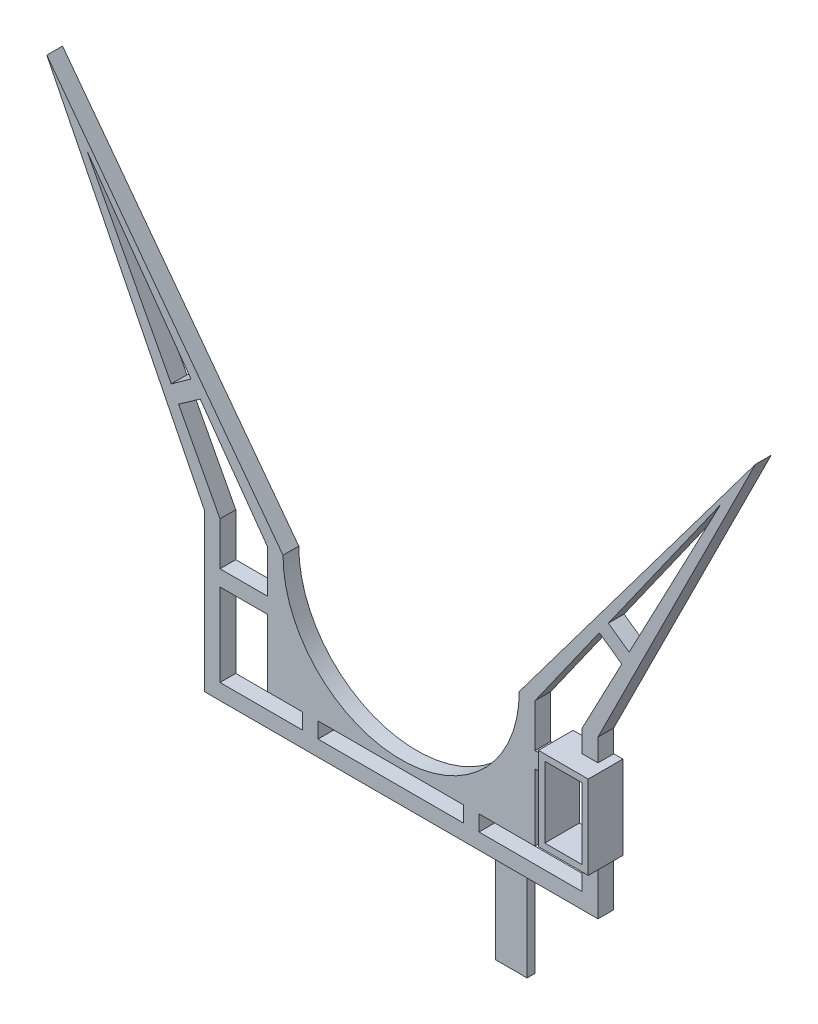
SolidWorks part; units mm, degrees
ref_plane "Front Plane" through (0, 0, 0) normal (0, 0, 1) x (1, 0, 0)
ref_plane "Top Plane" through (0, 0, 0) normal (0, 1, 0) x (1, 0, 0)
ref_plane "Right Plane" through (0, 0, 0) normal (1, 0, 0) x (0, 0, -1)
sketch "Sketch1" plane through (0, 0, 0) normal (0, 0, 1) x (1, 0, 0)
  line L0 (-112.5, 125) -> (-62.5, 25)
  line L1 (-62.5, -25) -> (62.5, -25)
  line L2 (-62.5, -25) -> (-62.5, 25)
  line L3 (-62.5, 25) -> (62.5, 25)
  line L4 (62.5, -25) -> (62.5, 25)
  line L5 (-62.5, -25) -> (62.5, 25) construction
  line L6 (-62.5, 25) -> (62.5, -25) construction
  line L7 (-37.5, 25) -> (-112.5, 25)
  line L8 (-37.5, 25) -> (-37.5, 125)
  line L9 (-37.5, 125) -> (-112.5, 125)
  line L10 (-112.5, 25) -> (-112.5, 125)
  line L11 (37.5, 25) -> (112.5, 25)
  line L12 (37.5, 25) -> (37.5, 125)
  line L13 (37.5, 125) -> (112.5, 125)
  line L14 (112.5, 25) -> (112.5, 125)
  line L15 (-112.5, 125) -> (-37.5, 25)
  line L16 (37.5, 25) -> (112.5, 125)
  line L17 (62.5, 25) -> (112.5, 125)
  arc A0 (37.5, 25) -> (-37.5, 25) centre (0, 25) cw
  point P0 (0, 0)
  dimension "D5" = 25
  dimension "D1" = 50
  dimension "D2" = 125
  dimension "D3" = 25
  dimension "D4" = 75
  dimension "D6" = 100
  dimension "D7" = 75
  dimension "D8" = 100
  dimension "D9" = 75
extrude "Boss-Extrude1" add sketch "Sketch1" along normal blind 5 contours L15 L0 L3 | L3 A0 L2 L1 L4 | L3 L17 L16
sketch "Sketch2" plane through (0, 0, 5) normal (0, 0, 1) x (1, 0, 0)
  line L10 (101.4139, 108.3538) -> (103.4554, 106.9108)
  line L15 (-42.5, -15) -> (42.5, -15)
  line L20 (57.5, -20) -> (-57.5, -20)
  line L21 (-62.5, -25) -> (62.5, -25) construction
  line L22 (-62.5, 25) -> (-37.5, 25)
  line L23 (37.5, 25) -> (62.5, 25)
  line L24 (-57.5, -20) -> (-57.5, 25)
  line L25 (-57.5, 25) -> (-99.7066, 105)
  line L26 (-99.7066, 105) -> (-42.5, 25)
  line L27 (-42.5, 25) -> (-42.5, -15)
  line L28 (42.5, -15) -> (42.5, 25)
  line L29 (42.5, 25) -> (101.4139, 108.3538)
  line L30 (101.4139, 108.3538) -> (57.5, 25)
  line L31 (57.5, 25) -> (57.5, -20)
  line L32 (-99.7066, 105) -> (-112.5, 125)
  line L33 (-99.7066, 105) -> (-101.9806, 103.9613)
  line L35 (-99.7066, 105) -> (-98.1256, 105.8341)
  line L36 (-112.5, 125) -> (-37.5, 25) construction
  line L37 (101.4139, 108.3538) -> (112.5, 125)
  line L38 (62.5, 25) -> (112.5, 125) construction
  line L40 (-112.5, 125) -> (-62.5, 25) construction
  dimension "D1" = 5
  dimension "D2" = 20
  dimension "D3" = 115
  dimension "D4" = 15
  dimension "D5" = 5
  dimension "D6" = 5
  dimension "D7" = 20
  dimension "D8" = 2.5
  dimension "D9" = 2.5
  dimension "D10" = 40
extrude "Cut-Extrude1" cut sketch "Sketch2" against normal blind 10 contours L31 L23 L28 L15 L27 L22 L24 L20 | L26 L25 L22 | L30 L29 L23
sketch "Sketch3" plane through (0, 0, 5) normal (0, 0, 1) x (1, 0, 0)
  line L0 (-42.5, -15) -> (42.5, -15) construction
  line L1 (-31.3776, -15) -> (-26.3776, -15)
  line L2 (-31.3776, -15) -> (-31.3776, -20)
  line L3 (-31.3776, -20) -> (-26.3776, -20)
  line L4 (-26.3776, -15) -> (-26.3776, -20)
  line L5 (57.5, -20) -> (-57.5, -20) construction
  line L6 (42.5, -15) -> (42.5, 25) construction
  line L7 (19.7255, -15) -> (24.7255, -15)
  line L8 (19.7255, -15) -> (19.7255, -20)
  line L9 (19.7255, -20) -> (24.7255, -20)
  line L10 (24.7255, -15) -> (24.7255, -20)
  line L11 (42.5, 11.2623) -> (57.5, 11.2623)
  line L12 (42.5, 11.2623) -> (42.5, 6.2623)
  line L13 (42.5, 6.2623) -> (57.5, 6.2623)
  line L14 (57.5, 11.2623) -> (57.5, 6.2623)
  line L15 (57.5, 25) -> (57.5, -20) construction
  line L16 (-57.5, -20) -> (-57.5, 25) construction
  line L17 (-57.5, 11.2623) -> (-42.5, 11.2623)
  line L18 (-57.5, 11.2623) -> (-57.5, 6.2623)
  line L19 (-57.5, 6.2623) -> (-42.5, 6.2623)
  line L20 (-42.5, 11.2623) -> (-42.5, 6.2623)
  line L21 (-42.5, 25) -> (-42.5, -15) construction
  line L22 (-70.6543, 49.9331) -> (-63.796, 54.7812)
  line L23 (-57.5, 25) -> (-99.7066, 105) construction
  line L24 (-99.7066, 105) -> (-42.5, 25) construction
  line L25 (-63.796, 54.7812) -> (-66.7044, 58.8483)
  line L26 (-66.7044, 58.8483) -> (-72.9874, 54.3554)
  line L27 (-72.9874, 54.3554) -> (-70.6543, 49.9331)
  line L28 (65.7866, 57.9469) -> (62.9252, 53.8984)
  line L30 (42.5, 25) -> (101.4139, 108.3538) construction
  line L32 (62.9252, 53.8984) -> (70.0659, 48.8515)
  line L33 (101.4139, 108.3538) -> (57.5, 25) construction
  line L34 (70.0659, 48.8515) -> (72.3964, 53.2751)
  line L35 (72.3964, 53.2751) -> (65.7866, 57.9469)
  dimension "D1" = 5
  dimension "D2" = 5
  dimension "D3" = 5
  dimension "D4" = 5
  dimension "D5" = 5
  dimension "D6" = 5
  dimension "D7" = 5
extrude "Boss-Extrude2" add sketch "Sketch3" against normal blind 5
sketch "Sketch5" plane through (0, 0, 0) normal (0, 0, -1) x (-1, 0, 0)
  line L5 (-37.5, -25) -> (-69, -25)
  line L6 (62.5, -25) -> (-62.5, -25) construction
  line L7 (-37.5, -25) -> (-37.5, -55)
  line L8 (-37.5, -55) -> (-69, -55)
  line L9 (-24.7255, -25) -> (-19.7255, -25)
  line L13 (-69, -25) -> (-69, -55)
  line L14 (-59, -25) -> (-27.5, -25)
  line L15 (-59, -25) -> (-59, -55)
  line L16 (-59, -55) -> (-27.5, -55)
  line L17 (31.3776, -25) -> (26.3776, -25)
  line L18 (-27.5, -25) -> (-27.5, -55)
  line L19 (62.5, -25) -> (-62.5, -25)
  dimension "D1" = 10
  dimension "D2" = 31.5
  dimension "D3" = 31.5
  dimension "D4" = 30
  dimension "D5" = 30
  dimension "D6" = 125
  dimension "D7" = 25
extrude "Boss-Extrude3" add sketch "Sketch5" against normal blind 2.5
sketch "Sketch6" plane through (0, 0, 5) normal (0, 0, 1) x (1, 0, 0)
  line L0 (37.5, 25) -> (37.5, 10)
  line L1 (37.5, 10) -> (57.5, 10)
  line L8 (63.4, 10) -> (57.5, 10)
  line L9 (51.6, 15.9) -> (63.4, 15.9)
  line L10 (51.6, 15.9) -> (51.6, -6.6)
  line L11 (51.6, -6.6) -> (63.4, -6.6)
  line L12 (63.4, 15.9) -> (63.4, -6.6)
  line L13 (57.5, 10) -> (51.6, 10)
  line L14 (49.6, 17.9) -> (65.4, 17.9)
  line L15 (49.6, 17.9) -> (49.6, -8.6)
  line L16 (49.6, -8.6) -> (65.4, -8.6)
  line L17 (65.4, 17.9) -> (65.4, -8.6)
  line M18 (57.5, 25) -> (57.5, 11.2623)
  line M19 (57.5, 11.2623) -> (42.5, 11.2623)
  line M40 (42.5, 6.2623) -> (57.5, 6.2623)
  line M41 (57.5, 6.2623) -> (57.5, -20)
  line M50 (62.5, -25) -> (62.5, 25)
  dimension "D1" = 15
  dimension "D2" = 20
  dimension "D3" = 5.9
  dimension "D4" = 5.9
  dimension "D5" = 5.9
  dimension "D6" = 16.6
  dimension "D7" = 2
  dimension "D8" = 2
  dimension "D9" = 2
  dimension "D10" = 2
extrude "Boss-Extrude6" add sketch "Sketch6" against normal blind 5 contours L9 L10 M19 M18 | L10 L1 L8 L9 M19 M50 M18 | L11 L8 L1 L10 M41 M50 M40 | L10 L11 M41 M40 | L17 L14 L9 L12 L11 L16 M50 | L14 L9 M18 M50 | L14 L15 L10 L9 M19 M18 | L15 L16 L11 L10 M41 M40 | L16 L11 M41 M50 | L1 L15 L10 M40 | L15 L1 L10 M19
sketch "Sketch7" plane through (0, 0, 5) normal (0, 0, 1) x (1, 0, 0)
  line L1 (62.5, 15.9) -> (63.4, 15.9)
  line L2 (62.5, 15.9) -> (62.5, -6.6)
  line L3 (62.5, -6.6) -> (63.4, -6.6)
  line L4 (63.4, 15.9) -> (63.4, -6.6)
extrude "Boss-Extrude7" add sketch "Sketch7" against normal blind 5
sketch "Sketch8" plane through (0, 0, 5) normal (0, 0, 1) x (1, 0, 0)
  line L0 (65.4, 17.9) -> (65.4, -8.6) construction
  line L1 (51.6, 15.9) -> (63.4, 15.9)
  line L2 (51.6, 15.9) -> (51.6, -6.6)
  line L3 (51.6, -6.6) -> (63.4, -6.6)
  line L4 (63.4, 15.9) -> (63.4, -6.6)
  line L5 (49.6, 17.9) -> (49.6, 11.2623) construction
  line L6 (49.6, 17.9) -> (57.5, 17.9) construction
  line L7 (49.6, -8.6) -> (57.5, -8.6) construction
  dimension "D1" = 2
  dimension "D2" = 2
  dimension "D3" = 2
  dimension "D4" = 2
extrude "Cut-Extrude2" cut sketch "Sketch8" against normal blind 5
sketch "Sketch9" plane through (0, 0, 5) normal (0, 0, 1) x (1, 0, 0)
  line L1 (51.6, 15.9) -> (63.4, 15.9)
  line L2 (51.6, 15.9) -> (51.6, -6.6)
  line L3 (51.6, -6.6) -> (63.4, -6.6)
  line L4 (63.4, 15.9) -> (63.4, -6.6)
  line L5 (49.6, 17.9) -> (65.4, 17.9)
  line L6 (49.6, 17.9) -> (49.6, -8.6)
  line L7 (49.6, -8.6) -> (65.4, -8.6)
  line L8 (65.4, 17.9) -> (65.4, -8.6)
extrude "Boss-Extrude8" add sketch "Sketch9" along normal blind 6
